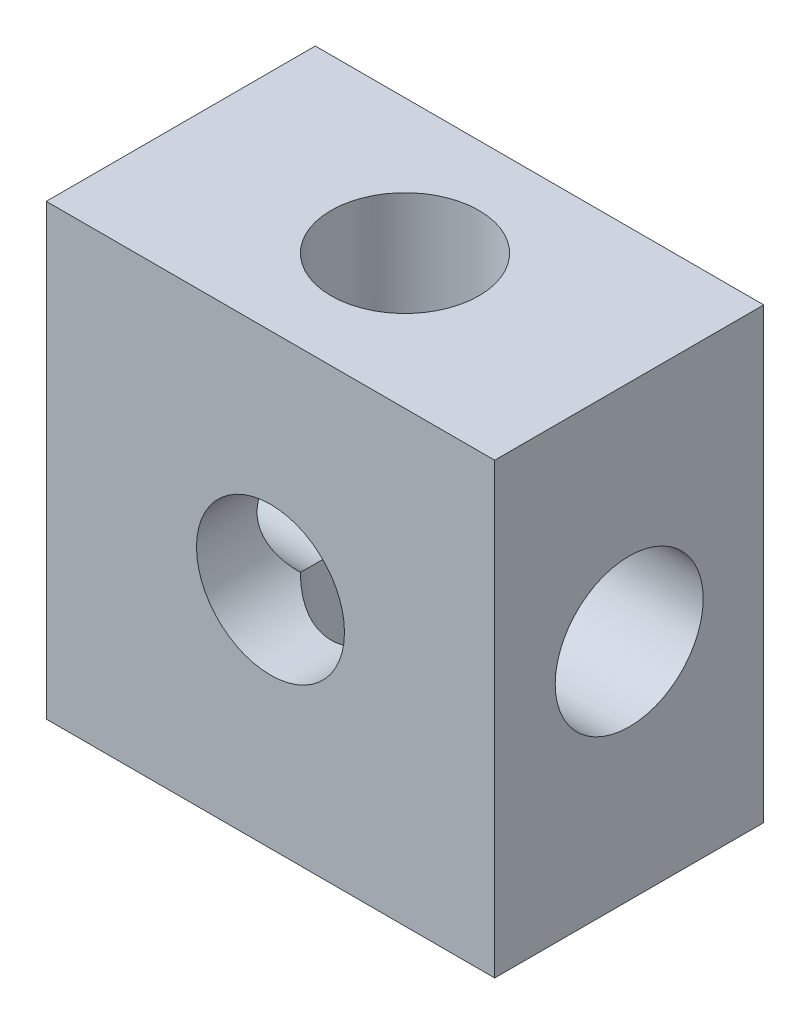
SolidWorks part; units mm, degrees
material "1060 合金"
ref_plane "前视基准面" through (0, 0, 0) normal (0, 0, 1) x (1, 0, 0)
ref_plane "上视基准面" through (0, 0, 0) normal (0, 1, 0) x (1, 0, 0)
ref_plane "右视基准面" through (0, 0, 0) normal (1, 0, 0) x (0, 0, -1)
sketch "草图1" plane through (0, 0, 0) normal (0, 0, 1) x (1, 0, 0)
  line L1 (-5, 5) -> (5, 5)
  line L2 (-5, 5) -> (-5, -5)
  line L3 (-5, -5) -> (5, -5)
  line L4 (5, 5) -> (5, -5)
  line L5 (-5, 5) -> (5, -5) construction
  line L6 (-5, -5) -> (5, 5) construction
  point P0 (0, 0)
  dimension "D1" = 10
extrude "凸台-拉伸1" add sketch "草图1" along normal blind 6
sketch "草图2" plane through (0, 0, 6) normal (0, 0, 1) x (1, 0, 0)
  circle A0 centre (0, 0) radius 1.65
  dimension "D1" = 3.3
extrude "切除-拉伸1" cut sketch "草图2" against normal blind 6
sketch "草图3" plane through (-5, 0, 0) normal (-1, 0, 0) x (0, 0, 1)
  line L0 (0, 0) -> (3, 0) construction
  circle A0 centre (3, 0) radius 1.65
  dimension "D2" = 3.3
  dimension "D1" = 3
extrude "切除-拉伸2" cut sketch "草图3" against normal through all both and the other way through all
sketch "草图4" plane through (0, 5, 0) normal (0, 1, 0) x (1, 0, 0)
  line L0 (0, 0) -> (0, -3) construction
  circle A0 centre (0, -3) radius 1.65
  dimension "D2" = 3.3
  dimension "D1" = 3
extrude "切除-拉伸3" cut sketch "草图4" against normal through all
